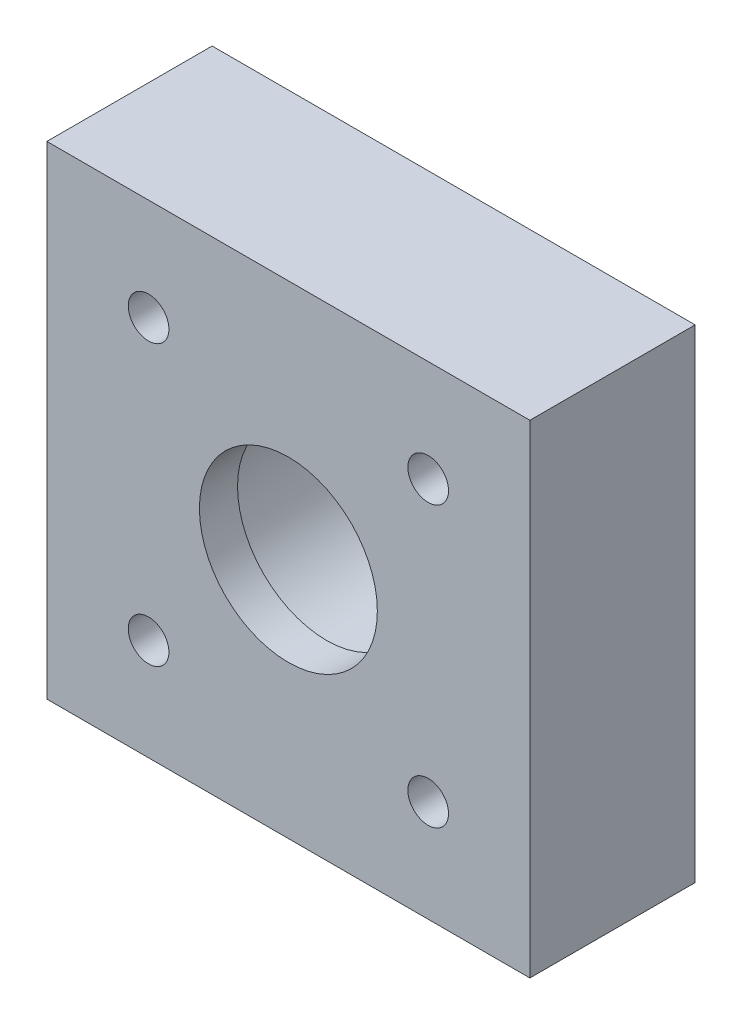
SolidWorks part; units mm, degrees
material "POM copolymère d'acétal"
ref_plane "Front Plane" through (0, 0, 0) normal (0, 0, 1) x (1, 0, 0)
ref_plane "Top Plane" through (0, 0, 0) normal (0, 1, 0) x (1, 0, 0)
ref_plane "Right Plane" through (0, 0, 0) normal (1, 0, 0) x (0, 0, -1)
sketch "Sketch1" plane through (0, 0, 0) normal (0, 0, 1) x (1, 0, 0)
  line L1 (9.5, -9.5) -> (-9.5, -9.5)
  line L2 (9.5, -9.5) -> (9.5, 9.5)
  line L3 (9.5, 9.5) -> (-9.5, 9.5)
  line L4 (-9.5, -9.5) -> (-9.5, 9.5)
  line L5 (9.5, -9.5) -> (-9.5, 9.5) construction
  line L6 (9.5, 9.5) -> (-9.5, -9.5) construction
  circle A0 centre (0, 0) radius 3.5
  point P0 (0, 0)
  dimension "D2" = 7
  dimension "D1" = 19
extrude "Boss-Extrude1" add sketch "Sketch1" along normal mid plane 6.5
hole_wizard "Tap Drill for M2 Tap1" positions "Sketch3" profile "Sketch2" hole size "M2" standard "DIN"
sketch "Sketch3" plane through (0, 0, 3.25) normal (0, 0, 1) x (1, 0, 0)
  line L7 (-5.5, 5.5) -> (-5.5, -5.5) construction
  line L10 (5.5, 5.5) -> (5.5, -5.5) construction
  line L12 (-5.5, 0) -> (5.5, 0) construction
  point P97 (-5.5, 5.5)
  point P101 (-5.5, -5.5)
  point P123 (5.5, 5.5)
  point P125 (5.5, -5.5)
  dimension "D1" = 11
  dimension "D2" = 11
sketch "Sketch2" plane through (-5.5, 5.5, 3.25) normal (1, 0, 0) x (0, -1, 0)
  line L0 (0, 0) -> (0, 11.5)
  line L1 (0, 11.5) -> (0.8, 11.5)
  line L2 (0.8, 11.5) -> (0.8, 0)
  line L5 (0.8, 0) -> (0, 0)
  line L10 (0, 11.5) -> (-0.8, 11.5) construction
  line L11 (0, -6.35) -> (0, 107.95) construction
  dimension "Hole Dia." = 1.6
  dimension "Hole Depth" = 11.5
  dimension "Drill Angle" = 180
sketch "Sketch4" plane through (0, 0, -3.25) normal (0, 0, -1) x (-1, 0, 0)
  circle A0 centre (0, 0) radius 4
  dimension "D1" = 8
extrude "Cut-Extrude1" cut sketch "Sketch4" against normal blind 5
